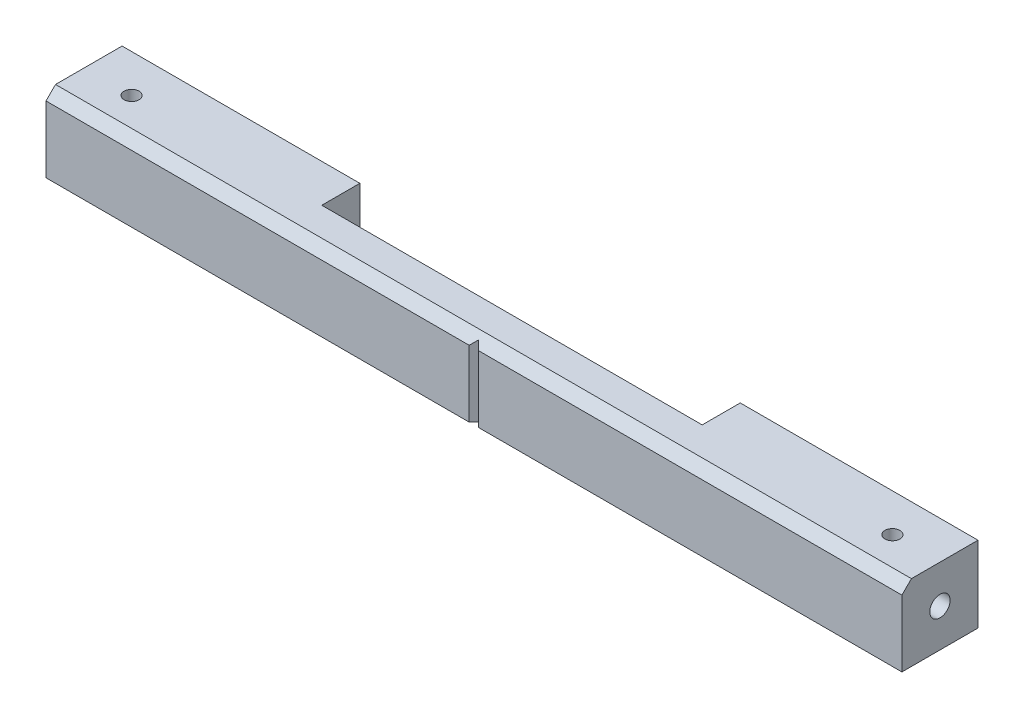
SolidWorks part; units mm, degrees
material "1060 Alloy"
ref_plane "Front Plane" through (0, 0, 0) normal (0, 0, 1) x (1, 0, 0)
ref_plane "Top Plane" through (0, 0, 0) normal (0, 1, 0) x (1, 0, 0)
ref_plane "Right Plane" through (0, 0, 0) normal (1, 0, 0) x (0, 0, -1)
sketch "ID_Width" plane through (0, 0, 0) normal (0, 1, 0) x (1, 0, 0)
  line L0 (-146.05, 0) -> (146.05, 0) construction
  dimension "D1" = 292.1
sketch "Cut_List" plane through (0, 0, 0) normal (0, 1, 0) x (1, 0, 0)
  line L0 (-141.2875, 0) -> (141.2875, 0) construction
  dimension "D1" = 282.575
sketch "Sketch1" plane through (0, 0, 0) normal (1, 0, 0) x (0, 0, -1)
  line L0 (-12.7, -12.7) -> (12.7, 12.7) construction
  line L1 (-12.7, 12.7) -> (12.7, 12.7)
  line L2 (-12.7, 12.7) -> (-12.7, -12.7)
  line L3 (-12.7, -12.7) -> (12.7, -12.7)
  line L4 (12.7, 12.7) -> (12.7, -12.7)
  dimension "D2" = 25.4
extrude "Extrude1" add sketch "Sketch1" along normal mid plane 285.75
hole_wizard "M8x1.25 Tapped Hole1" positions "Sketch3" profile "Sketch2" tap size "M8x1.25" standard "Ansi Metric"
sketch "Sketch3" plane through (142.875, 0, 0) normal (1, 0, 0) x (0, 0, -1)
  point P0 (0, 0)
cosmetic thread "Hole Thread1" parameters "D1"=16.002, "D2"=8
sketch "Sketch2" plane through (142.875, 0, 0) normal (0, 1, 0) x (0, 0, -1)
  line L0 (0, 0) -> (0, 21.8041)
  line L1 (0, 21.8041) -> (3.4, 19.7612)
  line L2 (3.4, 19.7612) -> (3.4, 0)
  line L5 (3.4, 0) -> (0, 0)
  line L10 (0, 21.8041) -> (-3.4, 19.7612) construction
  line L11 (0, -6.35) -> (0, 107.95) construction
  dimension "Tap Drill Dia." = 6.8
  dimension "Tap Drill Depth" = 19.7612
  dimension "Drill Angle" = 118
mirror "Mirror1" about plane through (0, 0, 0) normal (1, 0, 0) of "M8x1.25 Tapped Hole1"
chamfer "Chamfer1" distance 3.175 angle 45 1 edges at (0, 12.7, 12.7)
hole_wizard "M6x1.0 Tapped Hole1" positions "Sketch9" profile "Sketch8" tap size "M6x1.0" standard "Ansi Metric"
sketch "Sketch9" plane through (0, 12.7, 0) normal (0, 1, 0) x (-1, 0, 0)
  line L0 (127, 0) -> (-127, 0) construction
  line L1 (142.875, -12.7) -> (142.875, 9.525) construction
  point P0 (127, 0)
  point P1 (-127, 0)
  point P7 (0, 0)
  dimension "D1" = 15.875
sketch "Sketch8" plane through (-127, 12.7, 0) normal (1, 0, 0) x (0, 0, 1)
  line L0 (0, 0) -> (0, 16.4882)
  line L1 (0, 16.4882) -> (2.5, 14.986)
  line L2 (2.5, 14.986) -> (2.5, 0)
  line L5 (2.5, 0) -> (0, 0)
  line L10 (0, 16.4882) -> (-2.5, 14.986) construction
  line L11 (0, -6.35) -> (0, 107.95) construction
  dimension "Tap Drill Dia." = 5
  dimension "Tap Drill Depth" = 14.986
  dimension "Drill Angle" = 118
cosmetic thread "Hole Thread4" parameters "D1"=11.9888, "D2"=6
cosmetic thread "Hole Thread5" parameters "D1"=11.9888, "D2"=6
sketch "Sketch10" plane through (0, 12.7, 0) normal (0, 1, 0) x (1, 0, 0)
  line L0 (142.875, 12.7) -> (-142.875, 12.7) construction
  line L1 (-63.5, 12.7) -> (63.5, 12.7)
  line L2 (-63.5, 12.7) -> (-63.5, 0)
  line L3 (-63.5, 0) -> (63.5, 0)
  line L4 (63.5, 12.7) -> (63.5, 0)
  line L5 (142.875, -12.7) -> (-142.875, -12.7) construction
  point P6 (0, 0)
  dimension "D1" = 12.7
  dimension "D2" = 127
extrude "Cut-Extrude1" cut sketch "Sketch10" against normal up to next
sketch "Sketch11" plane through (0, -12.7, 0) normal (0, -1, 0) x (1, 0, 0)
  line L9 (-1.5875, 12.7) -> (1.5875, 12.7)
  line L10 (142.875, 12.7) -> (-142.875, 12.7) construction
  line L11 (1.5875, 12.7) -> (0, 11.1125)
  line L12 (0, 11.1125) -> (-1.5875, 12.7)
  point P4 (0, 12.7)
  dimension "D1" = 3.175
  dimension "D2" = 1.5875
extrude "Cut-Extrude2" cut sketch "Sketch11" against normal up to next
equation "\"D1@Cut_List\" = \"D1@ID_Width\" - 0.5 + 0.125"
